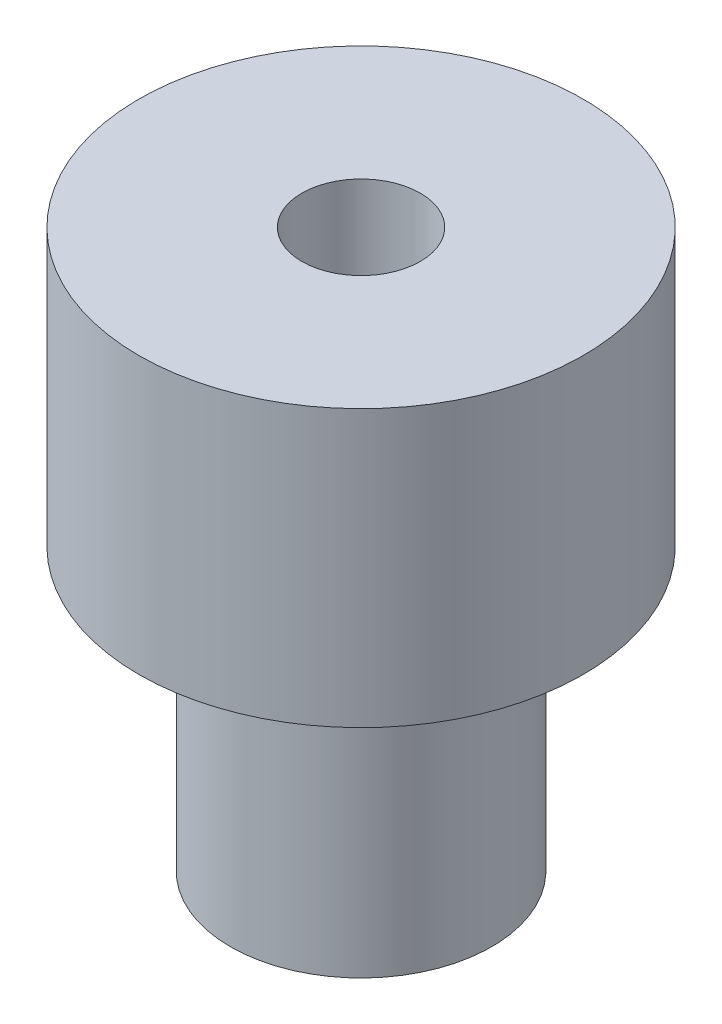
SolidWorks part; units mm, degrees
ref_plane "Front Plane" through (0, 0, 0) normal (0, 0, 1) x (1, 0, 0)
ref_plane "Top Plane" through (0, 0, 0) normal (0, 1, 0) x (1, 0, 0)
ref_plane "Right Plane" through (0, 0, 0) normal (1, 0, 0) x (0, 0, -1)
sketch "Sketch1" plane through (0, 0, 0) normal (0, 1, 0) x (1, 0, 0)
  circle A0 centre (0, 0) radius 5.95
  circle A1 centre (0, 0) radius 1.586
  dimension "D1" = 11.9
  dimension "D2" = 3.172
extrude "Boss-Extrude1" add sketch "Sketch1" along normal blind 7.4
sketch "Sketch2" plane through (0, 0, 0) normal (0, -1, 0) x (1, 0, 0)
  circle A0 centre (0, 0) radius 3.5
  circle A1 centre (0, 0) radius 1.586
  circle A2 centre (0, 0) radius 1.586 construction
  dimension "D1" = 7
extrude "Boss-Extrude2" add sketch "Sketch2" along normal blind 7.54
sketch "Sketch3" plane through (0, 0, 0) normal (1, 0, 0) x (0, 0, -1)
  line L0 (0, 0) -> (0, -7.54) construction
  line L1 (-3.5, -7.54) -> (3.5, -7.54) construction
  line L2 (-3.5, -3.77) -> (3.5, -3.77) construction
  line L3 (3.5, -7.54) -> (3.5, 0) construction
  circle A0 centre (0, -3.77) radius 1.25
  point P10 (0, -3.77)
  dimension "D1" = 2.5
extrude "Cut-Extrude1" cut sketch "Sketch3" against normal blind 10
